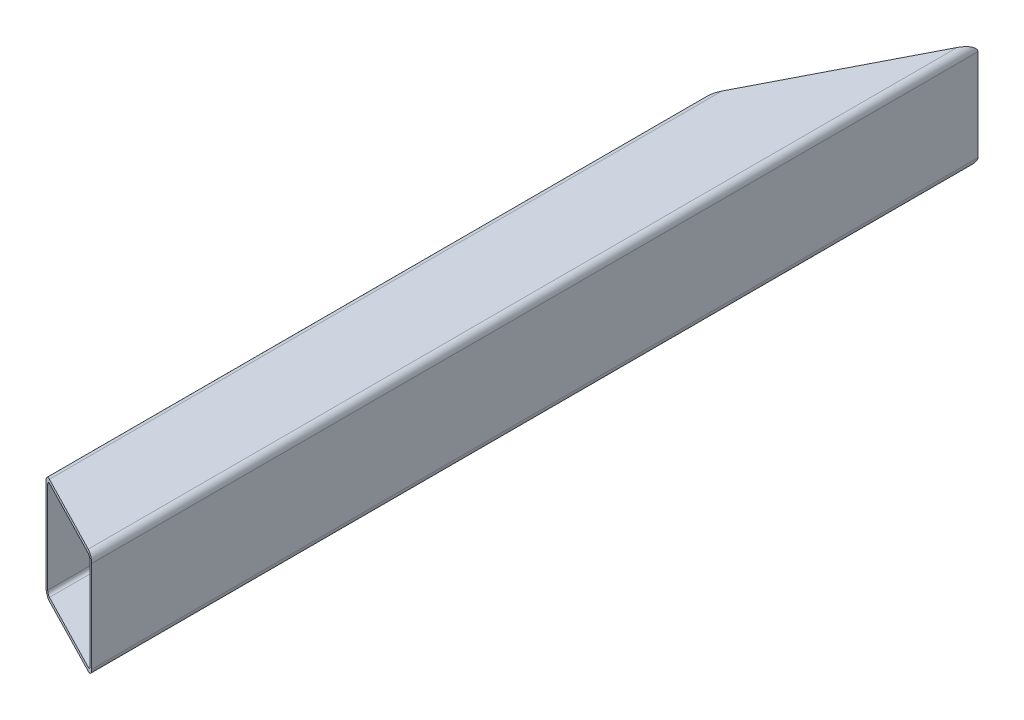
SolidWorks part; units mm, degrees
ref_plane "Спереди" through (0, 0, 0) normal (0, 0, 1) x (1, 0, 0)
ref_plane "Сверху" through (0, 0, 0) normal (0, 1, 0) x (1, 0, 0)
ref_plane "Справа" through (0, 0, 0) normal (1, 0, 0) x (0, 0, -1)
sketch "Эскиз1" plane through (0, 0, 0) normal (0, 0, 1) x (1, 0, 0)
  line L1 (34, 45) -> (-34, 45)
  line L2 (40, 39) -> (40, -39)
  line L3 (34, -45) -> (-34, -45)
  line L4 (-40, 39) -> (-40, -39)
  line L5 (40, 45) -> (-40, -45) construction
  line L6 (40, -45) -> (-40, 45) construction
  arc A0 (-40, -39) -> (-34, -45) centre (-34, -39) ccw
  arc A1 (34, -45) -> (40, -39) centre (34, -39) ccw
  arc A2 (40, 39) -> (34, 45) centre (34, 39) ccw
  arc A3 (-40, 39) -> (-34, 45) centre (-34, 39) cw
  point P0 (0, 0)
  dimension "D3" = 6
  dimension "D1" = 80
  dimension "D2" = 90
extrude "Вытянуть-Тонкостенный1" add sketch "Эскиз1" along normal blind 754 thin thin type one direction reverse wall 3
sketch "Эскиз2" plane through (0, 0, 0) normal (0, 1, 0) x (1, 0, 0)
  line L4 (40, 0) -> (-40, -155.5556)
  line L5 (-40, -754) -> (-40, 0) construction
  line L6 (40, -754) -> (40, 0) construction
  line L7 (40, -754) -> (-40, -712.8571)
  line L8 (-40, -155.5556) -> (-177.7521, 72.9134)
  line L9 (-177.7521, 72.9134) -> (175.5781, 72.9134)
  line L10 (175.5781, 72.9134) -> (175.5781, -903.0687)
  line L11 (175.5781, -903.0687) -> (-185.1646, -903.0687)
  line L12 (-185.1646, -903.0687) -> (-40, -712.8571)
  line L13 (40, -754) -> (40, 0)
  dimension "D3" = 27.216
  dimension "D5" = 62.784
extrude "Вырез-Вытянуть1" cut sketch "Эскиз2" against normal mid plane 120
